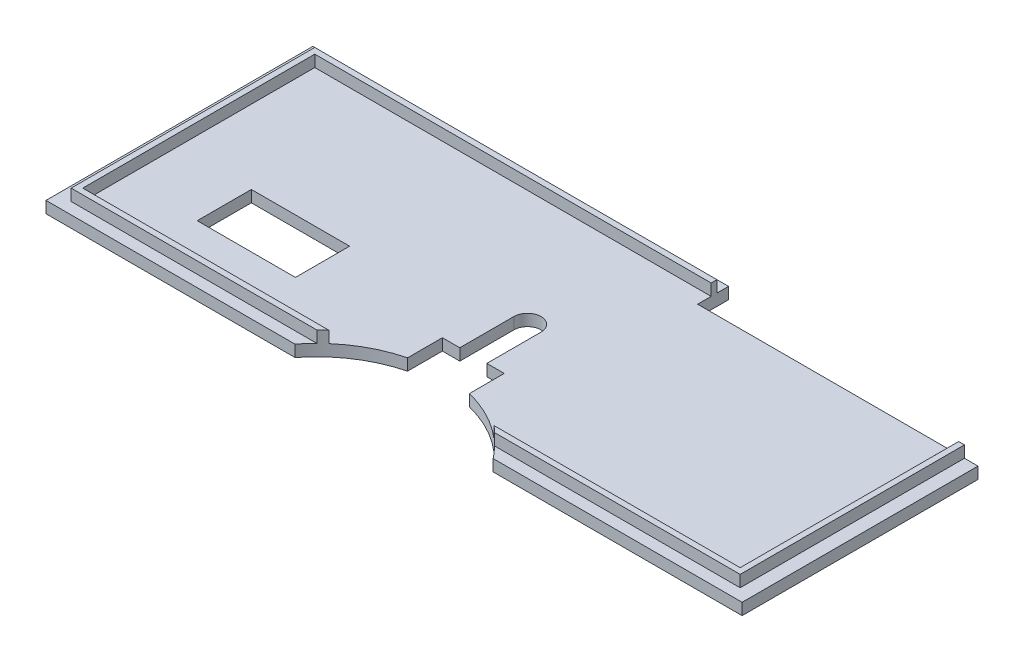
SolidWorks part; units mm, degrees
ref_plane "Front Plane" through (0, 0, 0) normal (0, 0, 1) x (1, 0, 0)
ref_plane "Top Plane" through (0, 0, 0) normal (0, 1, 0) x (1, 0, 0)
ref_plane "Right Plane" through (0, 0, 0) normal (1, 0, 0) x (0, 0, -1)
sketch "Sketch2" plane through (0, 0, 0) normal (0, 1, 0) x (1, 0, 0)
  line L1 (90, 34.5) -> (-90, 34.5)
  line L2 (90, 34.5) -> (90, -34.5)
  line L3 (90, -34.5) -> (-90, -34.5)
  line L4 (-90, 34.5) -> (-90, -34.5)
  line L5 (90, 34.5) -> (-90, -34.5) construction
  line L6 (90, -34.5) -> (-90, 34.5) construction
  point P0 (0, 0)
  dimension "D1" = 180
  dimension "D2" = 69
extrude "Boss-Extrude1" add sketch "Sketch2" along normal blind 3
sketch "Sketch3" plane through (0, 3, 0) normal (0, 1, 0) x (1, 0, 0)
  line L1 (86.5, 31.5) -> (-86.5, 31.5)
  line L2 (86.5, 31.5) -> (86.5, -31.5)
  line L3 (86.5, -31.5) -> (-86.5, -31.5)
  line L4 (-86.5, 31.5) -> (-86.5, -31.5)
  line L5 (86.5, 31.5) -> (-86.5, -31.5) construction
  line L6 (86.5, -31.5) -> (-86.5, 31.5) construction
  line L7 (85, 30) -> (-85, 30)
  line L8 (85, 30) -> (85, -30)
  line L9 (85, -30) -> (-85, -30)
  line L10 (-85, 30) -> (-85, -30)
  line L11 (85, 30) -> (-85, -30) construction
  line L12 (85, -30) -> (-85, 30) construction
  point P0 (0, 0)
  point P6 (0, 0)
  dimension "D1" = 173
  dimension "D2" = 63
  dimension "D3" = 170
  dimension "D4" = 60
extrude "Boss-Extrude2" add sketch "Sketch3" along normal blind 3
sketch "Sketch4" plane through (0, 0, 0) normal (0, -1, 0) x (1, 0, 0)
  line L0 (-90, 34.5) -> (90, 34.5) construction
  line L1 (-65.9, 34.5) -> (-40.5, 34.5)
  line L2 (-65.9, 34.5) -> (-65.9, -9.5)
  line L3 (-65.9, -9.5) -> (-40.5, -9.5)
  line L4 (-40.5, 34.5) -> (-40.5, -9.5)
  line L5 (-90, -34.5) -> (-90, 34.5) construction
  line L6 (-40.5, 12.5) -> (-65.9, 12.5) construction
  line L8 (-40.5, 5.5) -> (-65.9, 5.5)
  line L9 (-40.5, 5.5) -> (-40.5, 19.5)
  line L10 (-40.5, 19.5) -> (-65.9, 19.5)
  line L11 (-65.9, 5.5) -> (-65.9, 19.5)
  line L12 (-40.5, 5.5) -> (-65.9, 19.5) construction
  line L13 (-40.5, 19.5) -> (-65.9, 5.5) construction
  point P10 (-53.2, 12.5)
  dimension "D1" = 49.5
  dimension "D2" = 25.4
  dimension "D3" = 29
  dimension "D4" = 15
extrude "Cut-Extrude1" cut sketch "Sketch4" against normal blind 10 contours L4 L10 L2 L8
sketch "Sketch5" plane through (0, 6, 0) normal (0, 1, 0) x (1, 0, 0)
  line L0 (85, 30) -> (-85, 30) construction
  line L1 (86.5, 31.5) -> (17.5, 31.5)
  line L2 (86.5, 31.5) -> (86.5, 30)
  line L3 (86.5, 30) -> (17.5, 30)
  line L4 (17.5, 31.5) -> (17.5, 30)
  dimension "D1" = 69
extrude "Cut-Extrude2" cut sketch "Sketch5" against normal blind 3
sketch "Sketch6" plane through (0, 6, 0) normal (0, 1, 0) x (1, 0, 0)
  line L0 (85, -30) -> (85, 30) construction
  line L1 (86.5, 30) -> (85, 30)
  line L2 (86.5, 30) -> (86.5, 26.5)
  line L3 (86.5, 26.5) -> (85, 26.5)
  line L4 (85, 30) -> (85, 26.5)
  dimension "D1" = 3.5
extrude "Cut-Extrude3" cut sketch "Sketch6" against normal blind 3
sketch "Sketch7" plane through (0, 0, 0) normal (0, -1, 0) x (1, 0, 0)
  line L0 (0, 34.5) -> (0, -34.5) construction
  line L1 (-90, 34.5) -> (90, 34.5) construction
  line L2 (90, -34.5) -> (-90, -34.5) construction
  circle A0 centre (0, 0) radius 3.5
  dimension "D1" = 7
extrude "Cut-Extrude4" cut sketch "Sketch7" against normal blind 3
sketch "Sketch8" plane through (0, 0, 0) normal (0, -1, 0) x (1, 0, 0)
  line L0 (0, 34.5) -> (0, 54.5) construction
  line L1 (-90, 34.5) -> (90, 34.5) construction
  circle A0 centre (0, 54.5) radius 32.5
  dimension "D2" = 65
  dimension "D1" = 20
extrude "Cut-Extrude5" cut sketch "Sketch8" against normal blind 10
sketch "Sketch9" plane through (0, 0, 0) normal (0, -1, 0) x (1, 0, 0)
  line L1 (8, 30) -> (-8, 30)
  line L2 (8, 30) -> (8, 14)
  line L3 (8, 14) -> (-8, 14)
  line L4 (-8, 30) -> (-8, 14)
  line L5 (8, 30) -> (-8, 14) construction
  line L6 (8, 14) -> (-8, 30) construction
  arc A0 (-25.6174, 34.5) -> (25.6174, 34.5) centre (0, 54.5) ccw construction
  point P0 (0, 22)
  dimension "D1" = 16
  dimension "D2" = 16
extrude "Cut-Extrude6" cut sketch "Sketch9" against normal blind 10
sketch "Sketch10" plane through (0, 3, 0) normal (0, 1, 0) x (1, 0, 0)
  line L0 (17.5, 31.5) -> (17.5, 30) construction
  line L1 (90, 34.5) -> (17.5, 34.5)
  line L2 (90, 34.5) -> (90, 26.5)
  line L3 (90, 26.5) -> (17.5, 26.5)
  line L4 (17.5, 34.5) -> (17.5, 26.5)
  line L5 (85, 26.5) -> (86.5, 26.5) construction
  point P5 (17.5, 30.5)
  dimension "D1" = 0
  dimension "D2" = 0
extrude "Cut-Extrude7" cut sketch "Sketch10" against normal blind 10
sketch "Sketch11" plane through (0, 0, 0) normal (0, -1, 0) x (-1, 0, 0)
  line L0 (8, -14) -> (-8, -14) construction
  line L1 (3.5, 0) -> (-3.5, 0)
  line L2 (3.5, 0) -> (3.5, -14)
  line L3 (3.5, -14) -> (-3.5, -14)
  line L4 (-3.5, 0) -> (-3.5, -14)
  circle A0 centre (0, 0) radius 3.5 construction
extrude "Cut-Extrude8" cut sketch "Sketch11" against normal blind 10
